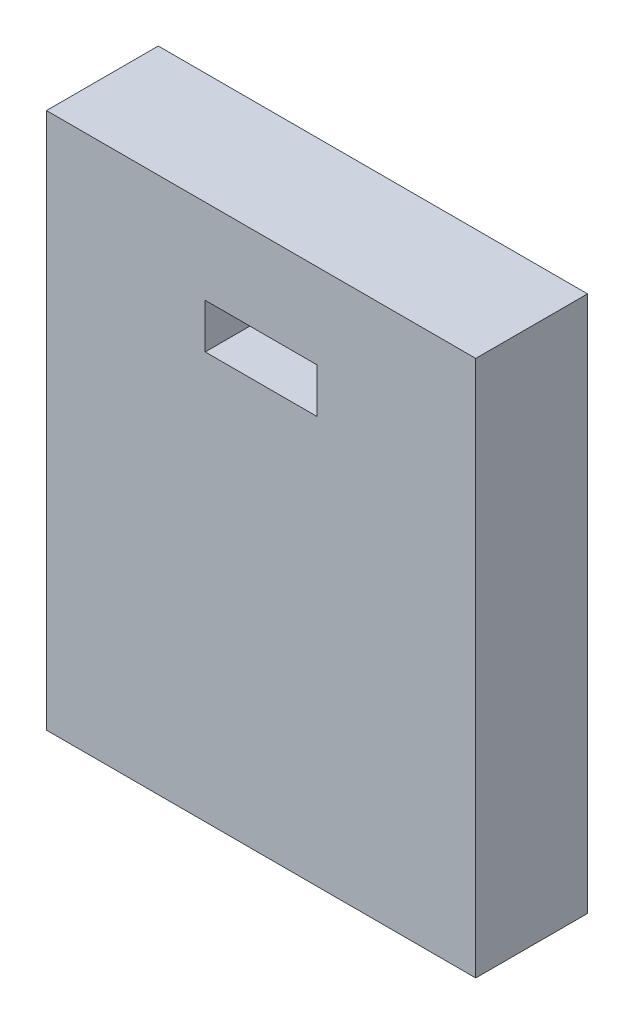
SolidWorks part; units mm, degrees
material "Oak"
ref_plane "Front" through (0, 0, 0) normal (0, 0, 1) x (1, 0, 0)
ref_plane "Top" through (0, 0, 0) normal (0, 1, 0) x (1, 0, 0)
ref_plane "Right" through (0, 0, 0) normal (1, 0, 0) x (0, 0, -1)
sketch "Sketch1" plane through (0, 0, 0) normal (0, 0, 1) x (1, 0, 0)
  line L1 (0, 0) -> (12.192, 0)
  line L2 (0, 0) -> (0, 15.24)
  line L3 (0, 15.24) -> (12.192, 15.24)
  line L4 (12.192, 0) -> (12.192, 15.24)
  dimension "D1" = 12.192
  dimension "D2" = 15.24
extrude "Boss-Extrude1" add sketch "Sketch1" along normal blind 3.175
sketch "Sketch2" plane through (0, 0, 3.175) normal (0, 0, 1) x (1, 0, 0)
  line L0 (6.096, 12.827) -> (6.096, 11.557) construction
  line L1 (4.5085, 11.557) -> (7.6835, 11.557)
  line L2 (4.5085, 11.557) -> (4.5085, 12.827)
  line L3 (4.5085, 12.827) -> (7.6835, 12.827)
  line L4 (7.6835, 11.557) -> (7.6835, 12.827)
  line L5 (0, 15.24) -> (0, 0) construction
  dimension "D1" = 1.27
  dimension "D2" = 11.557
  dimension "D3" = 6.096
  dimension "D4" = 3.175
extrude "Cut-Extrude1" cut sketch "Sketch2" against normal blind 3.175
